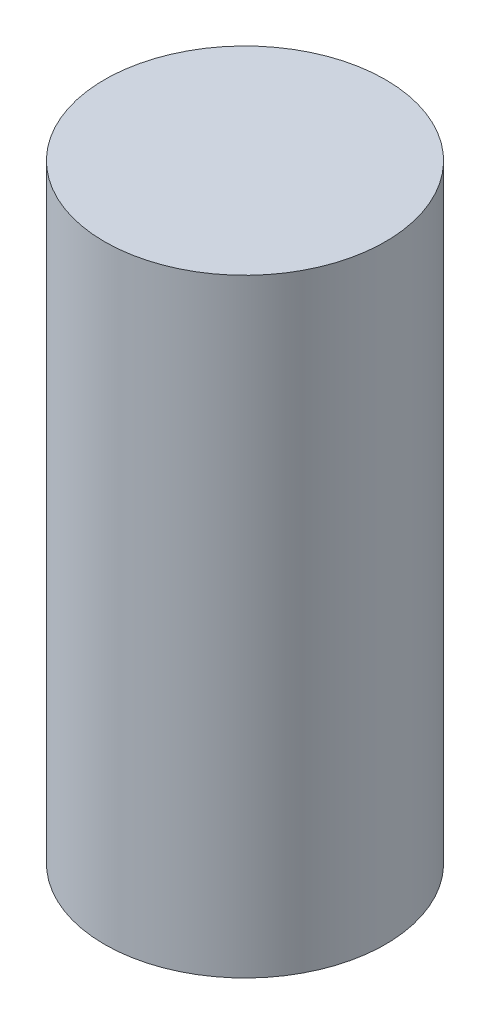
SolidWorks part; units mm, degrees
ref_plane "Front Plane" through (0, 0, 0) normal (0, 0, 1) x (1, 0, 0)
ref_plane "Top Plane" through (0, 0, 0) normal (0, 1, 0) x (1, 0, 0)
ref_plane "Right Plane" through (0, 0, 0) normal (1, 0, 0) x (0, 0, -1)
sketch "Sketch1" plane through (0, 0, 0) normal (0, 1, 0) x (1, 0, 0)
  circle A0 centre (0, 0) radius 3
  dimension "D1" = 6
extrude "Boss-Extrude1" add sketch "Sketch1" along normal blind 13
